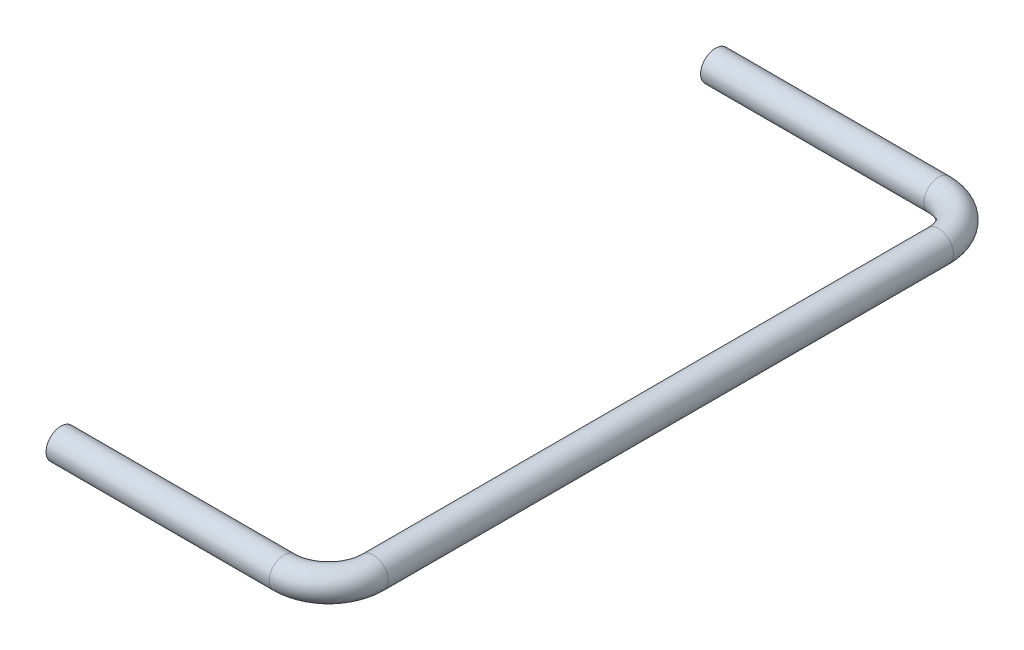
SolidWorks part; units mm, degrees
ref_plane "Спереди" through (0, 0, 0) normal (0, 0, 1) x (1, 0, 0)
ref_plane "Сверху" through (0, 0, 0) normal (0, 1, 0) x (1, 0, 0)
ref_plane "Справа" through (0, 0, 0) normal (1, 0, 0) x (0, 0, -1)
sketch "Эскиз1" plane through (0, 0, 0) normal (1, 0, 0) x (0, 0, -1)
  circle A0 centre (0, 0) radius 1
sketch3d "Трехмерный эскиз1"
  line L0 (0, 0, 0) -> (15, 0, 0)
  line L1 (18, 0, -3) -> (18, 0, -41)
  line L2 (15, 0, -44) -> (0, 0, -44)
  arc A0 (15, 0, 0) -> (18, 0, -3) centre (15, 0, -3) ccw
  arc A1 (18, 0, -41) -> (15, 0, -44) centre (15, 0, -41) ccw
  point P7 (18, 0, 0)
  point P8 (15, 3, -3)
  point P11 (18, 0, -44)
  point P12 (15, 3, -41)
  dimension "D1" = 3
sweep "По траектории1" add profiles "Эскиз1" path "Трехмерный эскиз1"
